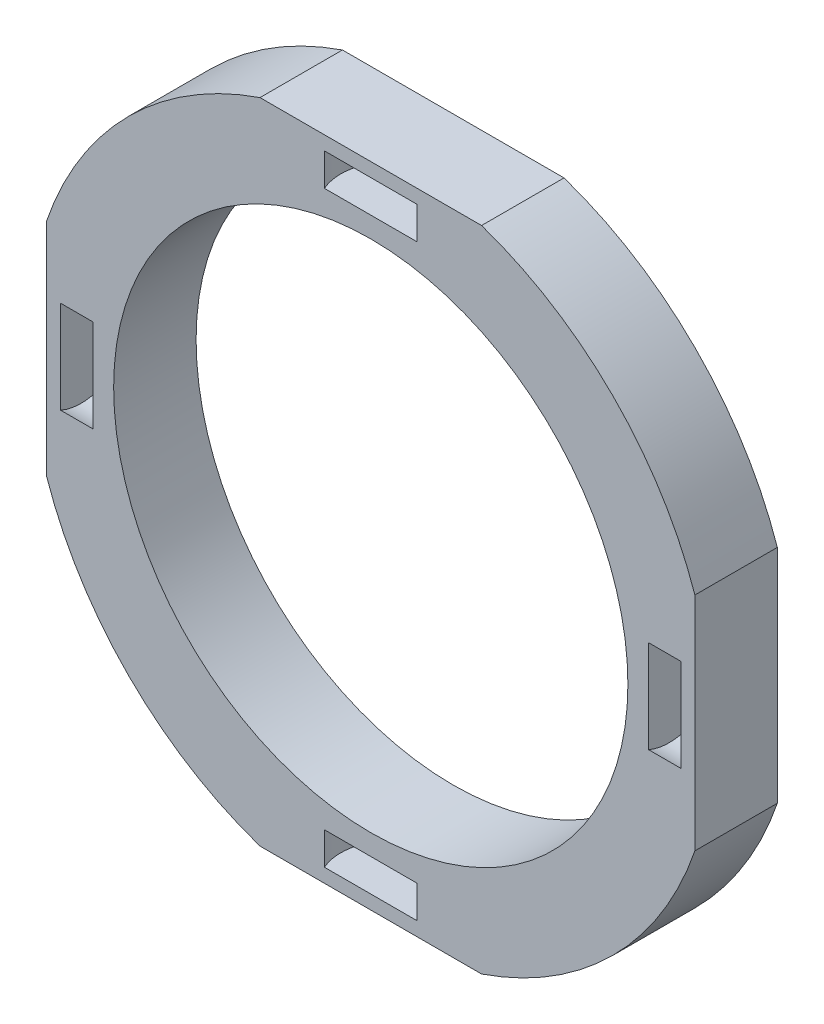
SolidWorks part; units mm, degrees
ref_plane "Front Plane" through (0, 0, 0) normal (0, 0, 1) x (1, 0, 0)
ref_plane "Top Plane" through (0, 0, 0) normal (0, 1, 0) x (1, 0, 0)
ref_plane "Right Plane" through (0, 0, 0) normal (1, 0, 0) x (0, 0, -1)
sketch "Sketch1" plane through (0, 0, 0) normal (0, 0, 1) x (1, 0, 0)
  line L0 (0, 0) -> (15.9766, -2.5) construction
  line L1 (-15.9766, 2.5) -> (-12.6746, 2.5) construction
  line L2 (-15.9766, 2.5) -> (-15.9766, -2.5) construction
  line L3 (-15.9766, -2.5) -> (-12.6746, -2.5) construction
  line L4 (-12.6746, 2.5) -> (-12.6746, -2.5) construction
  line L5 (-15.9766, 2.5) -> (-12.6746, -2.5) construction
  line L6 (-15.9766, -2.5) -> (-12.6746, 2.5) construction
  line L7 (12.6746, 2.5) -> (15.9766, 2.5) construction
  line L8 (12.6746, 2.5) -> (12.6746, -2.5) construction
  line L9 (12.6746, -2.5) -> (15.9766, -2.5) construction
  line L10 (15.9766, 2.5) -> (15.9766, -2.5) construction
  line L11 (12.6746, 2.5) -> (15.9766, -2.5) construction
  line L12 (12.6746, -2.5) -> (15.9766, 2.5) construction
  line L13 (-15.9766, 5.4611) -> (-15.9766, -5.4611)
  line L14 (5.4611, 15.9766) -> (-5.4611, 15.9766)
  line L15 (15.9766, -5.4611) -> (15.9766, 5.4611)
  line L16 (-5.4611, -15.9766) -> (5.4611, -15.9766)
  circle A0 centre (0, 0) radius 12.6746
  circle A1 centre (0, 0) radius 16.8842
  point P4 (-14.3256, 0)
  point P9 (14.3256, 0)
  point P16 (0, 0)
  point P27 (0, 0)
  dimension "D1" = 25.3492
  dimension "D6" = 4
  dimension "D2" = 5
  dimension "D3" = 3.302
  dimension "D4" = 16.171
extrude "Boss-Extrude1" add sketch "Sketch1" along normal blind 1.016 and the other way blind 3.048
sketch "Sketch3" plane through (0, 0, 0) normal (0, 0, 1) x (1, 0, 0)
  line L0 (-15.9766, -2.5) -> (-12.6746, -2.5) construction
  line L1 (-13.6906, -2.5) -> (-15.2908, -2.5)
  line L2 (-13.6906, -2.5) -> (-13.6906, 0)
  line L3 (-13.6906, 0) -> (-15.2908, 0)
  line L4 (-15.2908, -2.5) -> (-15.2908, 0)
  line L5 (-12.6746, 2.5) -> (-12.6746, -2.5) construction
  dimension "D1" = 1.6002
  dimension "D2" = 1.016
revolve "Cut-Revolve2" cut sketch "Sketch3" angle 360 about L3
pattern_circular "CirPattern1" count 4 over 360 about axis through (0, 0, 0) along (0, 0, 1) of "Cut-Revolve2"
